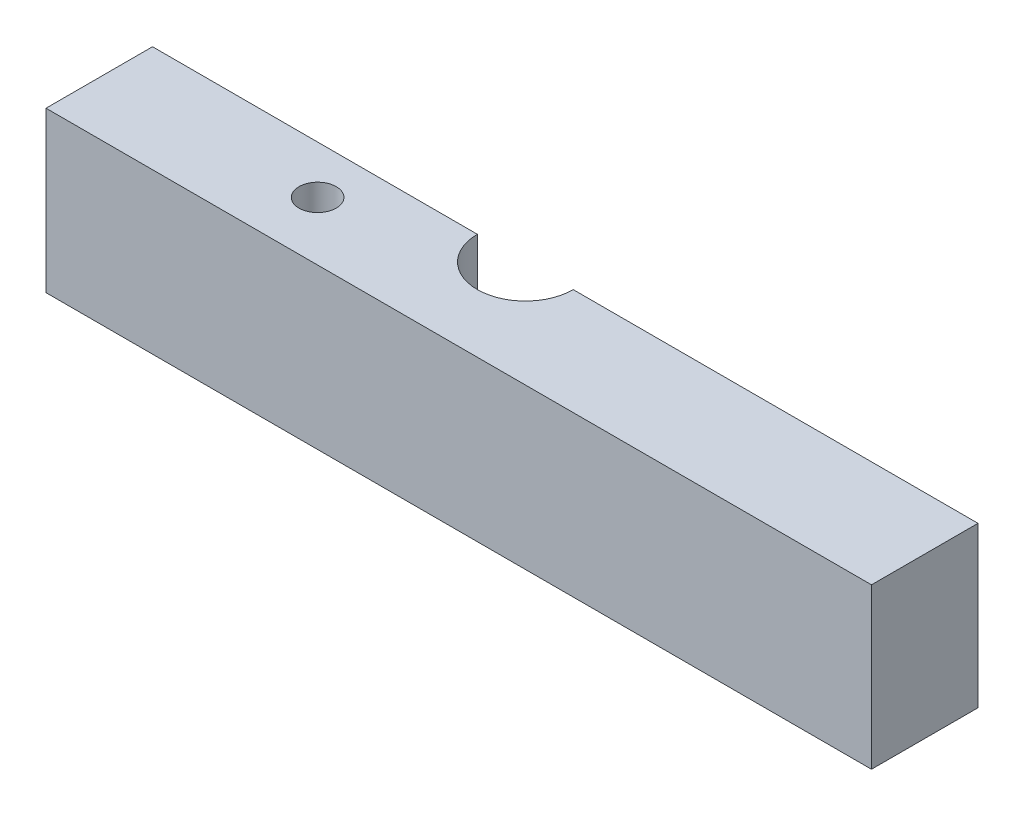
SolidWorks part; units mm, degrees
ref_plane "Front" through (0, 0, 0) normal (0, 0, 1) x (1, 0, 0)
ref_plane "Top" through (0, 0, 0) normal (0, 1, 0) x (1, 0, 0)
ref_plane "Right" through (0, 0, 0) normal (1, 0, 0) x (0, 0, -1)
sketch "Sketch1" plane through (0, 0, 0) normal (0, 1, 0) x (1, 0, 0)
  line L1 (-70, 20) -> (85, 20)
  line L2 (-70, 20) -> (-70, -20)
  line L3 (-70, -20) -> (85, -20)
  line L4 (85, 20) -> (85, -20)
  circle A0 centre (0, 0) radius 9
  point P8 (-70, 0)
  dimension "D1" = 18
  dimension "D2" = 40
  dimension "D3" = 155
  dimension "D4" = 70
extrude "Boss-Extrude1" add sketch "Sketch1" along normal blind 30
ref_plane "Plane1" through (0, 0, 0) normal (0, 0, 1) x (1, 0, 0)
sketch "Sketch3" plane through (0, 30, 0) normal (0, 1, 0) x (1, 0, 0)
  line L0 (-11.9063, 2.5) -> (-11.9063, -2.5)
  line L3 (11.9062, 2.5) -> (11.9062, -2.5)
  line L5 (-11.9063, 2.5) -> (-15.0813, 2.5)
  line L6 (-11.9063, 2.5) -> (-11.9063, -2.5)
  line L7 (-11.9063, -2.5) -> (-15.0813, -2.5)
  line L8 (-15.0813, 2.5) -> (-15.0813, -2.5)
  line L9 (11.9062, 2.5) -> (15.0812, 2.5)
  line L10 (11.9062, 2.5) -> (11.9062, -2.5)
  line L11 (11.9062, -2.5) -> (15.0812, -2.5)
  line L12 (15.0812, 2.5) -> (15.0812, -2.5)
  line L13 (-70, 0) -> (85, 0) construction
  line L14 (-70, 20) -> (-70, -20) construction
  line L15 (85, -20) -> (85, 20) construction
  circle A0 centre (0, 0) radius 9 construction
  circle A1 centre (0, 0) radius 9
  circle A3 centre (0, 0) radius 11.9062
  point P6 (-15.0813, 0)
  point P19 (15.0812, 0)
  dimension "D1" = 23.8125
  dimension "D2" = 3.175
  dimension "D3" = 5
sketch "Sketch2" plane through (0, 0, 0) normal (0, 0, 1) x (1, 0, 0)
  line L4 (-70, 0) -> (85, 0)
  line L5 (85, 0) -> (85, 30)
  line L6 (85, 30) -> (-70, 30)
  line L7 (-70, 30) -> (-70, 0)
  line L8 (-70, 0) -> (85, 0)
  line L9 (85, 0) -> (85, 30)
  line L10 (85, 30) -> (-70, 30)
  line L11 (-70, 30) -> (-70, 0)
  dimension "D1" = 0
extrude "Cut-Extrude1" cut sketch "Sketch2" against normal through all
sketch "Sketch4" plane through (0, 0, 0) normal (0, -1, 0) x (1, 0, 0)
  line L2 (-70, 9) -> (85, 9) construction
  line L3 (-70, 0) -> (-70, 20) construction
  line L4 (85, 20) -> (85, 0) construction
  circle A0 centre (-30, 9) radius 3.5
  arc A2 (9, 0) -> (-9, 0) centre (0, 0) ccw construction
  dimension "D1" = 7
  dimension "D2" = 30
extrude "Cut-Extrude3" cut sketch "Sketch4" against normal through all
equation "\"Length\"= 155mm'Match working Model"
equation "\"D3@Sketch1\"= \"Length\""
equation "\"ΔTCPC\"= 30mm'Between 0-5cm (Working Models should have minimum of 2cm already to reach the 2-7cm ΔTCPC specifications )in 0.5cm increments"
equation "\"D1@Boss-Extrude1\" = \"ΔTCPC\""
equation "\"Width\"= 40.00mm'Match working Model"
equation "\"D2@Sketch1\"=\"Width\""
